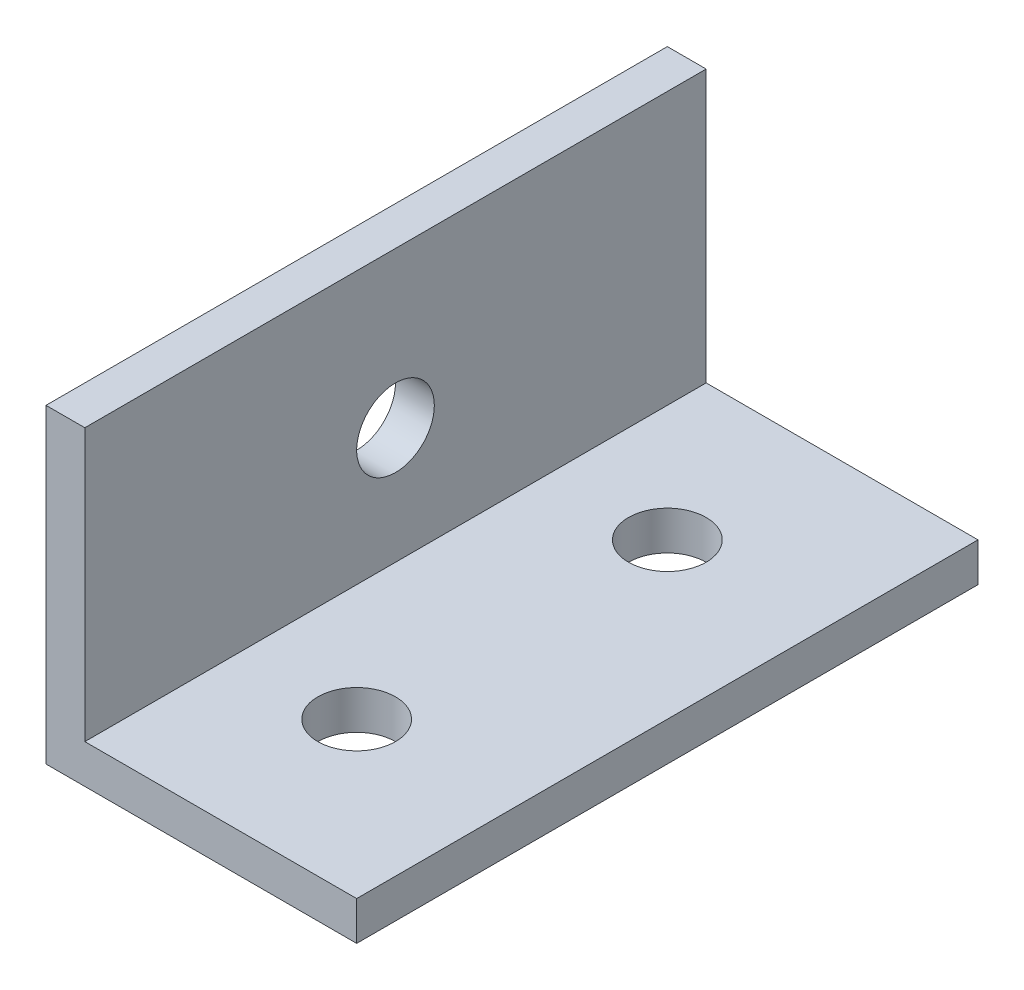
SolidWorks part; units mm, degrees
ref_plane "Front Plane" through (0, 0, 0) normal (0, 0, 1) x (1, 0, 0)
ref_plane "Top Plane" through (0, 0, 0) normal (0, 1, 0) x (1, 0, 0)
ref_plane "Right Plane" through (0, 0, 0) normal (1, 0, 0) x (0, 0, -1)
sketch "Sketch1" plane through (0, 0, 0) normal (0, 0, 1) x (1, 0, 0)
  line L0 (0, 0) -> (25.4, 0)
  line L1 (25.4, 0) -> (25.4, 3.175)
  line L2 (25.4, 3.175) -> (3.175, 3.175)
  line L3 (3.175, 3.175) -> (3.175, 25.4)
  line L4 (3.175, 25.4) -> (0, 25.4)
  line L5 (0, 25.4) -> (0, 0)
  dimension "D1" = 25.4
  dimension "D2" = 25.4
  dimension "D3" = 22.225
  dimension "D4" = 22.225
extrude "Boss-Extrude1" add sketch "Sketch1" along normal blind 50.8
sketch "Sketch2" plane through (3.175, 0, 0) normal (1, 0, 0) x (0, 0, -1)
  line L0 (-50.8, 3.175) -> (-50.8, 25.4) construction
  line L1 (-50.8, 3.175) -> (0, 3.175) construction
  circle A0 centre (-25.4, 12.7) radius 3.175
  point P4 (0, 0)
  dimension "D1" = 6.35
  dimension "D2" = 25.4
  dimension "D3" = 9.525
extrude "Cut-Extrude1" cut sketch "Sketch2" against normal through all
sketch "Sketch3" plane through (0, 3.175, 0) normal (0, 1, 0) x (1, 0, 0)
  line L0 (25.4, -50.8) -> (3.175, -50.8) construction
  line L1 (25.4, 0) -> (3.175, 0) construction
  line L2 (3.175, -50.8) -> (3.175, 0) construction
  circle A0 centre (12.7, -38.1) radius 3.175
  circle A1 centre (12.7, -12.7) radius 3.175
  point P4 (0, 0)
  dimension "D3" = 6.35
  dimension "D1" = 12.7
  dimension "D2" = 12.7
  dimension "D4" = 9.525
extrude "Cut-Extrude2" cut sketch "Sketch3" against normal through all
